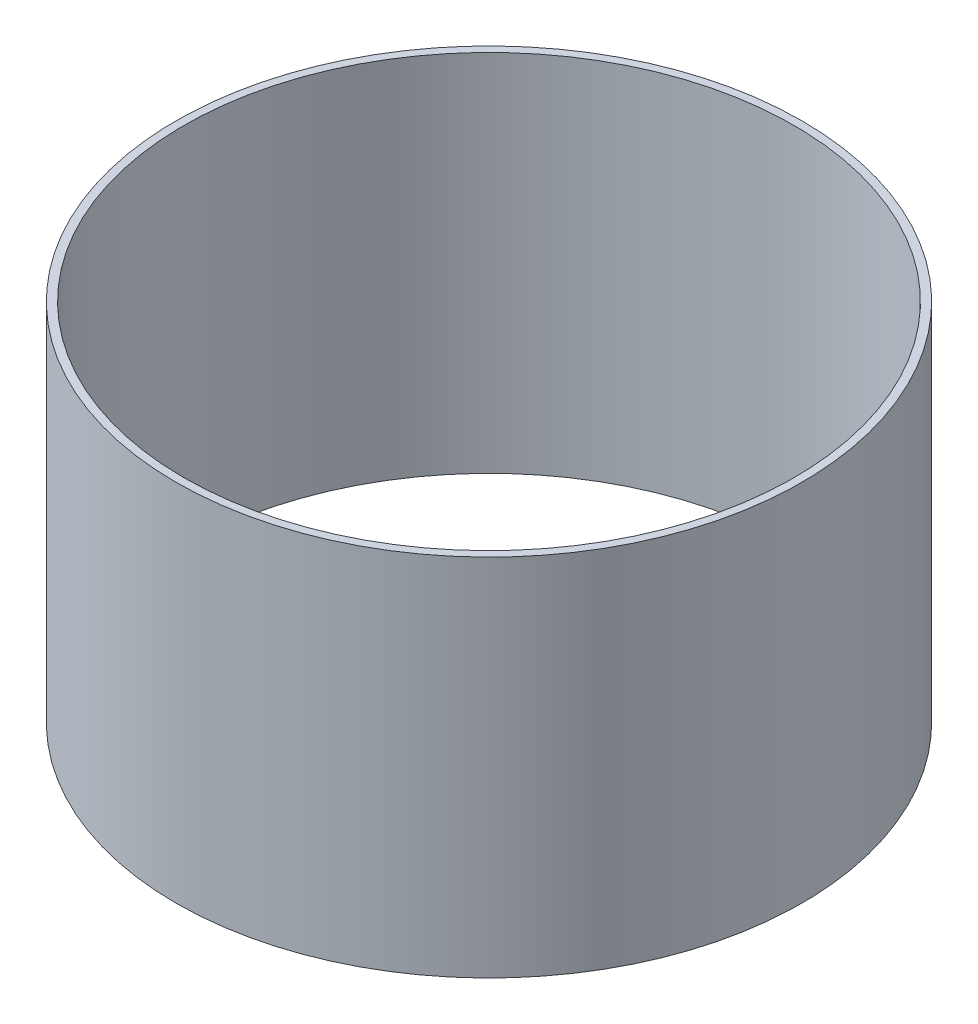
SolidWorks part; units mm, degrees
ref_plane "Front Plane" through (0, 0, 0) normal (0, 0, 1) x (1, 0, 0)
ref_plane "Top Plane" through (0, 0, 0) normal (0, 1, 0) x (1, 0, 0)
ref_plane "Right Plane" through (0, 0, 0) normal (1, 0, 0) x (0, 0, -1)
sketch "Sketch1" plane through (0, 0, 0) normal (0, 1, 0) x (1, 0, 0)
  circle A0 centre (0, 0) radius 79
  circle A1 centre (0, 0) radius 77
  dimension "D1" = 158
  dimension "D2" = 154
extrude "Boss-Extrude1" add sketch "Sketch1" along normal blind 92
